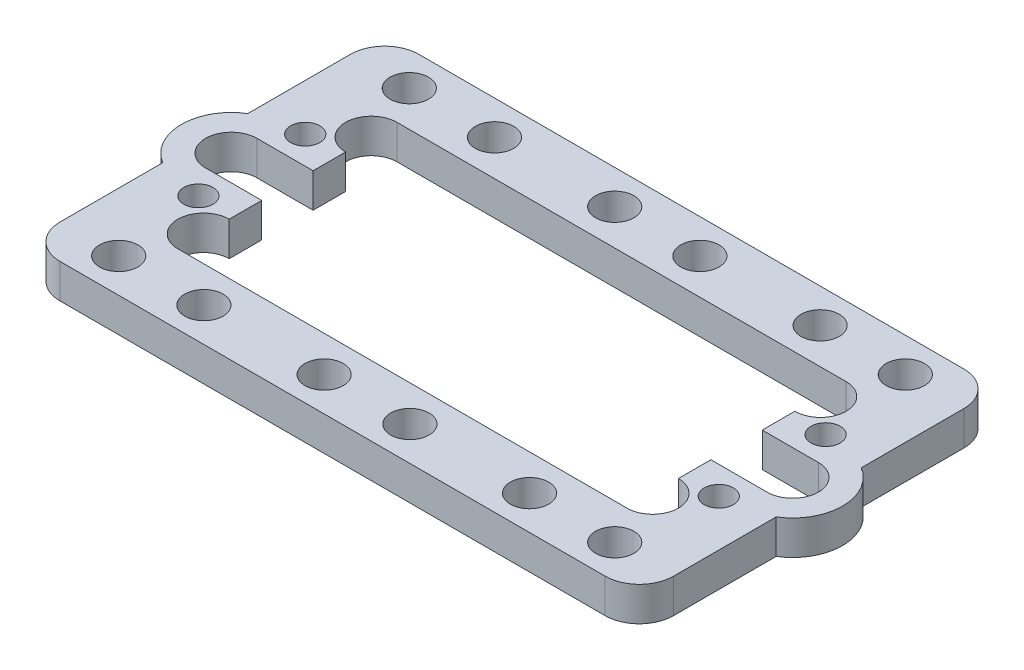
SolidWorks part; units mm, degrees
ref_plane "Front Plane" through (0, 0, 0) normal (0, 0, 1) x (1, 0, 0)
ref_plane "Top Plane" through (0, 0, 0) normal (0, 1, 0) x (1, 0, 0)
ref_plane "Right Plane" through (0, 0, 0) normal (1, 0, 0) x (0, 0, -1)
sketch "Sketch1" plane through (0, 0, 0) normal (0, 1, 0) x (1, 0, 0)
  line L0 (-28.448, 16.637) -> (28.448, -16.637) construction
  line L1 (-28.448, 16.637) -> (28.448, 16.637)
  line L2 (-28.448, 16.637) -> (-28.448, -16.637) construction
  line L3 (-28.448, -16.637) -> (28.448, -16.637)
  line L4 (28.448, 16.637) -> (28.448, -16.637) construction
  line L5 (-26.035, 0) -> (26.035, 0) construction
  line L6 (-28.448, 16.637) -> (-28.448, 3.9431)
  line L7 (-28.448, -3.9431) -> (-28.448, -16.637)
  line L8 (28.448, -3.9431) -> (28.448, -16.637)
  line L9 (28.448, 16.637) -> (28.448, 3.9431)
  arc A0 (28.448, 3.9431) -> (28.448, -3.9431) centre (26.035, 0) cw
  arc A1 (-28.448, 3.9431) -> (-28.448, -3.9431) centre (-26.035, 0) ccw
  dimension "D4" = 4.6228
  dimension "D1" = 56.896
  dimension "D2" = 33.274
  dimension "D3" = 52.07
extrude "Mass" add sketch "Sketch1" along normal blind 3.175
sketch "Sketch2" plane through (0, 3.175, 0) normal (0, 1, 0) x (1, 0, 0)
  line L0 (-26.035, 0) -> (26.035, 0) construction
  line L1 (-20.828, -10.16) -> (20.828, -10.16)
  line L2 (-20.828, -10.16) -> (-20.828, 10.16) construction
  line L3 (-20.828, 10.16) -> (20.828, 10.16)
  line L4 (20.828, -10.16) -> (20.828, 10.16) construction
  line L5 (-20.828, -10.16) -> (20.828, 10.16) construction
  line L6 (-20.828, 10.16) -> (20.828, -10.16) construction
  line L7 (-26.035, 2.3813) -> (26.035, 2.3813)
  line L8 (-26.035, -2.3813) -> (26.035, -2.3812)
  line L9 (-20.828, 5.3975) -> (-20.828, -5.3975)
  line L10 (20.828, 5.3975) -> (20.828, -5.3975)
  arc A0 (-26.035, 2.3813) -> (-26.035, -2.3813) centre (-26.035, 0) ccw
  arc A1 (26.035, -2.3812) -> (26.035, 2.3813) centre (26.035, 0) ccw
  arc A2 (20.828, 10.16) -> (20.828, 5.3975) centre (20.828, 7.7788) cw
  arc A3 (20.828, -10.16) -> (20.828, -5.3975) centre (20.828, -7.7788) ccw
  arc A4 (-20.828, -10.16) -> (-20.828, -5.3975) centre (-20.828, -7.7788) cw
  arc A5 (-20.828, 10.16) -> (-20.828, 5.3975) centre (-20.828, 7.7787) ccw
  point P0 (0, 0)
  point P8 (0, 0)
  dimension "D5" = 2.3813
  dimension "D1" = 41.656
  dimension "D2" = 20.32
  dimension "D3" = 52.07
extrude "Servo Hole" cut sketch "Sketch2" against normal through all contours A4 L1 A3 L10 L8 L9 | L10 L7 L9 L8 | L3 A5 L9 L7 L10 A2 | L8 A1 L7 L10 | L7 A0 L8 L9
hole_wizard "#6-32 Servo Mount" positions "Sketch4" profile "Sketch3" tap size "#6-32" standard "ANSI Inch"
sketch "Sketch4" plane through (0, 3.175, 0) normal (0, 1, 0) x (1, 0, 0)
  line L1 (-24.13, 4.953) -> (24.13, 4.953) construction
  line L2 (-24.13, 4.953) -> (-24.13, -4.953) construction
  line L3 (-24.13, -4.953) -> (24.13, -4.953) construction
  line L4 (24.13, 4.953) -> (24.13, -4.953) construction
  line L6 (-24.13, -4.953) -> (24.13, 4.953) construction
  point P0 (24.13, 4.953)
  point P2 (24.13, -4.953)
  point P4 (-24.13, -4.953)
  point P6 (-24.13, 4.953)
  dimension "D1" = 48.26
  dimension "D2" = 9.906
sketch "Sketch3" plane through (24.13, 3.175, -4.953) normal (1, 0, 0) x (0, 0, 1)
  line L0 (0, 0) -> (0, 153.2127)
  line L1 (0, 153.2127) -> (1.3525, 152.4)
  line L2 (1.3525, 152.4) -> (1.3525, 0)
  line L5 (1.3525, 0) -> (0, 0)
  line L10 (0, 153.2127) -> (-1.3526, 152.4) construction
  line L11 (0, -6.35) -> (0, 107.95) construction
  dimension "Tap Drill Dia." = 2.7051
  dimension "Tap Drill Depth" = 152.4
  dimension "Drill Angle" = 118
cosmetic thread "Hole Thread1" parameters "D1"=3.175, "D2"=3.5052
cosmetic thread "Hole Thread2" parameters "D1"=3.175, "D2"=3.5052
cosmetic thread "Hole Thread3" parameters "D1"=3.175, "D2"=3.5052
cosmetic thread "Hole Thread4" parameters "D1"=3.175, "D2"=3.5052
fillet "Corners" radius 3.175 4 edges at (28.448, 1.5875, -16.637) (28.448, 1.5875, 16.637) (-28.448, 1.5875, -16.637) (-28.448, 1.5875, 16.637)
sketch "Sketch5" plane through (0, 3.175, 0) normal (0, 1, 0) x (1, 0, 0)
  line L1 (22.9997, 13.4747) -> (-22.9997, 13.4747) construction
  line L2 (22.9997, 13.4747) -> (22.9997, -13.4747) construction
  line L3 (22.9997, -13.4747) -> (-22.9997, -13.4747) construction
  line L4 (-22.9997, 13.4747) -> (-22.9997, -13.4747) construction
  line L5 (22.9997, 13.4747) -> (-22.9997, -13.4747) construction
  line L6 (22.9997, -13.4747) -> (-22.9997, 13.4747) construction
  circle A0 centre (-22.9997, 13.4747) radius 1.778
  circle A1 centre (22.9997, 13.4747) radius 1.778
  circle A2 centre (22.9997, -13.4747) radius 1.778
  circle A3 centre (-22.9997, -13.4747) radius 1.778
  circle A4 centre (-15.1003, 13.4747) radius 1.778
  circle A5 centre (-3.9497, 13.4747) radius 1.778
  circle A6 centre (3.9497, 13.4747) radius 1.778
  circle A7 centre (15.1003, 13.4747) radius 1.778
  circle A8 centre (15.1003, -13.4747) radius 1.778
  circle A9 centre (4.0005, -13.4747) radius 1.778
  circle A10 centre (-3.9497, -13.4747) radius 1.778
  circle A11 centre (-15.1003, -13.4747) radius 1.778
  point P0 (0, 0)
  dimension "D3" = 3.556
  dimension "D1" = 26.9494
  dimension "D2" = 45.9994
  dimension "D4" = 7.8994
  dimension "D5" = 7.8994
  dimension "D6" = 11.1506
  dimension "D7" = 11.1506
  dimension "D8" = 7.8994
  dimension "D9" = 7.8994
  dimension "D10" = 11.1506
  dimension "D11" = 11.0998
extrude "Mounting Holes" cut sketch "Sketch5" against normal through all
